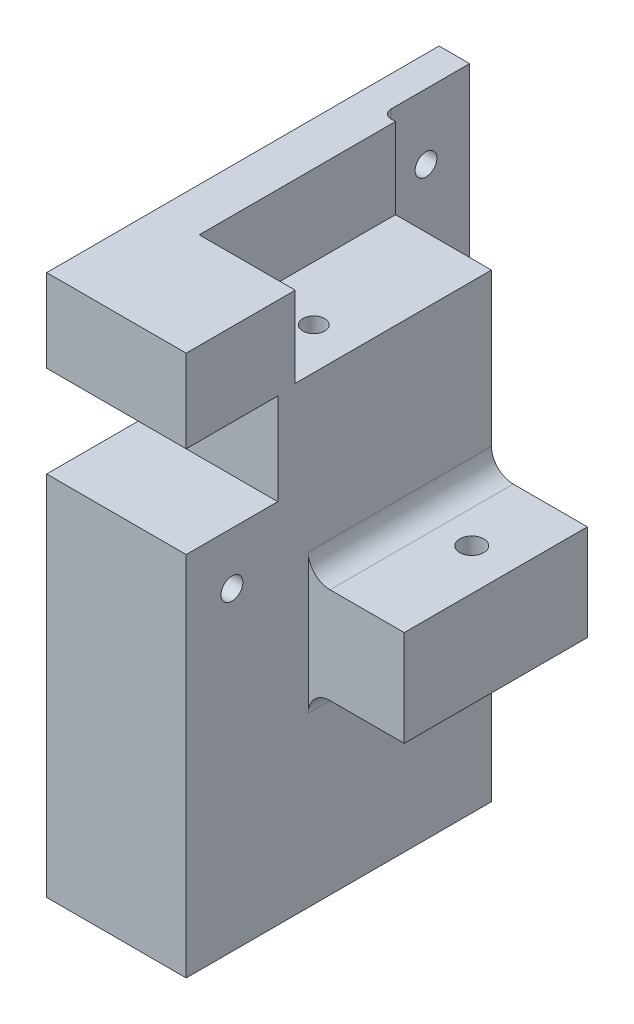
SolidWorks part; units mm, degrees
ref_plane "Front" through (0, 0, 0) normal (0, 0, 1) x (1, 0, 0)
ref_plane "Top" through (0, 0, 0) normal (0, 1, 0) x (1, 0, 0)
ref_plane "Right" through (0, 0, 0) normal (1, 0, 0) x (0, 0, -1)
sketch "Sketch1" plane through (0, 0, 0) normal (0, 1, 0) x (1, 0, 0)
  line L1 (-16, 35) -> (16, 35)
  line L2 (-16, 35) -> (-16, -35)
  line L3 (-16, -35) -> (16, -35)
  line L4 (16, 35) -> (16, -35)
  line L5 (-16, 35) -> (16, -35) construction
  line L6 (-16, -35) -> (16, 35) construction
  point P0 (0, 0)
  dimension "D1" = 70
  dimension "D2" = 32
extrude "Boss-Extrude1" add sketch "Sketch1" against normal blind 84.1 and the other way blind 40
sketch "Sketch2" plane through (0, 0, 0) normal (1, 0, 0) x (0, 0, -1)
  line L0 (-35, 40) -> (-35, -84.1) construction
  line L8 (-35, 0) -> (-14, 21) construction
  line L9 (-35, 21) -> (-14, 0) construction
  line L10 (-14, 21) -> (-14, 0)
  line L11 (-35, 0) -> (-14, 0)
  line L12 (-35, 21) -> (-35, 0)
  line L13 (-35, 21) -> (-14, 21)
  point P2 (0, 0)
  point P3 (-24.5, 10.5)
  point P22 (-24.5, 10.5)
  dimension "D1" = 21
extrude "Cut-Extrude1" cut sketch "Sketch2" against normal through all both and the other way through all
sketch "Sketch3" plane through (0, 40, 0) normal (0, 1, 0) x (1, 0, 0)
  line L1 (16, -35) -> (16, 35) construction
  line L3 (16, 35) -> (-16, 35) construction
  line L7 (-6, 35) -> (16, 35)
  line L8 (-6, 35) -> (-6, -10)
  line L9 (-6, -10) -> (16, -10)
  line L10 (16, 35) -> (16, -10)
  dimension "D1" = 45
  dimension "D2" = 22
extrude "Cut-Extrude2" cut sketch "Sketch3" against normal up to surface (18.5 mm away)
sketch "Sketch4" plane through (16, 0, 0) normal (1, 0, 0) x (0, 0, -1)
  line L6 (-7, -40.5) -> (35, -40.5)
  line L8 (-7, -18.5) -> (-7, -40.5)
  line L9 (35, -18.5) -> (-7, -18.5)
  line L10 (35, -40.5) -> (35, -18.5)
  line L11 (-10, 21.5) -> (35, 21.5) construction
  line L12 (35, 21.5) -> (35, -84.1) construction
  dimension "D1" = 42
  dimension "D2" = 22
  dimension "D3" = 40
extrude "Boss-Extrude2" add sketch "Sketch4" along normal blind 22
sketch "Sketch5" plane through (0, -18.5, 0) normal (0, 1, 0) x (1, 0, 0)
  line L3 (38, 35) -> (16, 35) construction
  line L4 (16, -35) -> (16, 35) construction
  circle A1 centre (28.5, 18) radius 2.75
  point P0 (28.3727, 17.8902)
  dimension "D2" = 12.5
  dimension "D3" = 5.5
  dimension "D1" = 17
extrude "Cut-Extrude3" cut sketch "Sketch5" against normal through all
sketch "Sketch6" plane through (0, 0, -35) normal (0, 0, 1) x (1, 0, 0)
  line L0 (-16, 40) -> (-9, 40)
  line L1 (-16, 40) -> (16, 40) construction
  line L2 (-9, 40) -> (-9, -25)
  line L3 (-9, -25) -> (-16, -25)
  line L4 (-16, 40) -> (-16, 21) construction
  line L5 (-16, -25) -> (-16, 40)
  dimension "D1" = 7
  dimension "D2" = 65
extrude "Boss-Extrude3" add sketch "Sketch6" against normal blind 20
sketch "Sketch7" plane through (0, 0, 0) normal (-1, 0, 0) x (0, 0, 1)
  line L4 (35, 0) -> (14, 0) construction
  circle A0 centre (24.5, -12) radius 2.5
  point P2 (22.5485, 0)
  point P3 (0, 0)
  point P4 (25.2528, -15.7988)
  point P8 (24.5, 0)
  dimension "D1" = 5
  dimension "D2" = 12
extrude "Cut-Extrude4" cut sketch "Sketch7" against normal through all both and the other way through all
sketch "Sketch8" plane through (-9, 0, 0) normal (1, 0, 0) x (0, 0, -1)
  line L1 (55, 40) -> (35, 40) construction
  line L2 (55, -25) -> (35, -25) construction
  circle A0 centre (45, 25) radius 2.5
  circle A1 centre (45, -10) radius 2.5
  point P4 (45, -9.1829)
  point P11 (45, 40)
  dimension "D1" = 5
  dimension "D2" = 15
  dimension "D3" = 15
extrude "Cut-Extrude5" cut sketch "Sketch8" against normal through all
fillet "Fillet1" radius 2 1 edges at (-9, 7.5, -35)
fillet "Fillet2" radius 5 3 edges at (16, -18.5, -14) (16, -40.5, -14) (-11.5, -25, -35)
sketch "Sketch9" plane through (0, 21.5, 0) normal (0, 1, 0) x (1, 0, 0)
  line L3 (-6, 35) -> (-6, -10) construction
  line L5 (-6, -10) -> (16, -10) construction
  circle A1 centre (6.5, 3.75) radius 2.5
  dimension "D2" = 13.75
  dimension "D3" = 5
  dimension "D1" = 12.5
extrude "Cut-Extrude6" cut sketch "Sketch9" against normal blind 47.45
